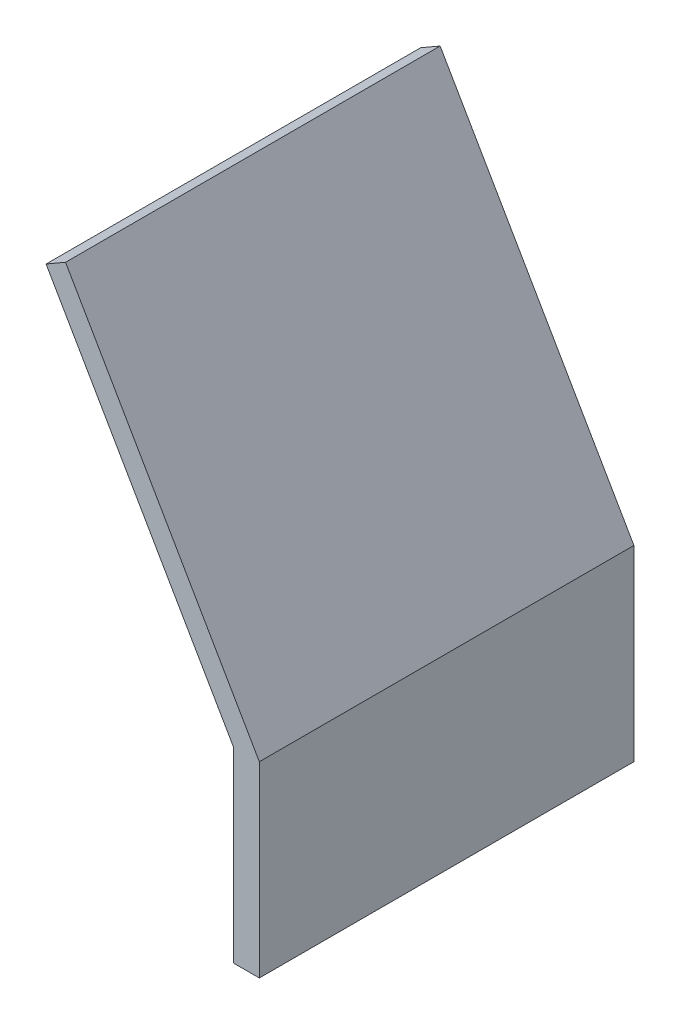
SolidWorks part; units mm, degrees
ref_plane "Front Plane" through (0, 0, 0) normal (0, 0, 1) x (1, 0, 0)
ref_plane "Top Plane" through (0, 0, 0) normal (0, 1, 0) x (1, 0, 0)
ref_plane "Right Plane" through (0, 0, 0) normal (1, 0, 0) x (0, 0, -1)
sketch "Sketch2" plane through (0, 0, 0) normal (0, 0, 1) x (1, 0, 0)
  line L0 (-28.4641, 43.3013) -> (-3.4641, 0)
  line L2 (0, 0) -> (-25.866, 44.8013)
  line L3 (-25.866, 44.8013) -> (-28.4641, 43.3013)
  line L4 (0, 0) -> (0, 44.8013) construction
  line L5 (0, 44.8013) -> (-25.866, 44.8013) construction
  line L8 (0, 0) -> (0, -25)
  line L9 (0, -25) -> (-3.4641, -25)
  line L10 (-3.4641, 0) -> (-3.4641, -25)
  point P4 (0, 0)
  point P8 (-8.0411, -33.2866)
  point P10 (0, 0)
  dimension "D1" = 50
  dimension "D2" = 3
  dimension "D3" = 30
  dimension "D4" = 25
extrude "Boss-Extrude1" add sketch "Sketch2" along normal mid plane 50
